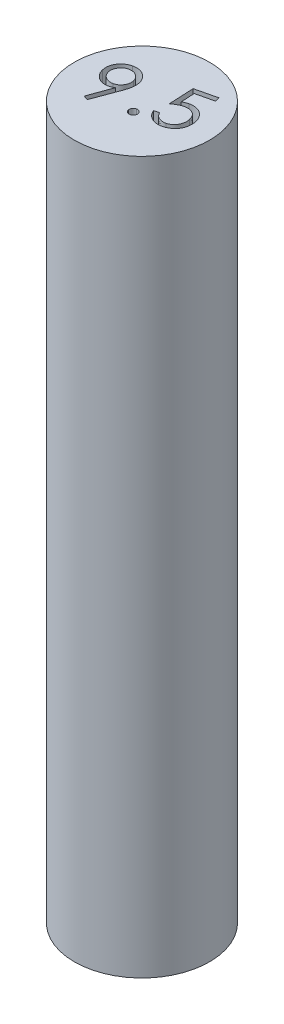
SolidWorks part; units mm, degrees
ref_plane "Front Plane" through (0, 0, 0) normal (0, 0, 1) x (1, 0, 0)
ref_plane "Top Plane" through (0, 0, 0) normal (0, 1, 0) x (1, 0, 0)
ref_plane "Right Plane" through (0, 0, 0) normal (1, 0, 0) x (0, 0, -1)
sketch "Sketch1" plane through (0, 0, 0) normal (0, 1, 0) x (1, 0, 0)
  circle A0 centre (0, 0) radius 4.75
  dimension "D1" = 9.5
extrude "Boss-Extrude1" add sketch "Sketch1" along normal blind 50
sketch "Sketch2" plane through (0, 50, 0) normal (0, 1, 0) x (1, 0, 0)
  line L0 (-3.8944, -2.1859) -> (4.5158, -0.1887) construction
  text T0 "9.5"
extrude "Cut-Extrude1" cut sketch "Sketch2" against normal blind 3
